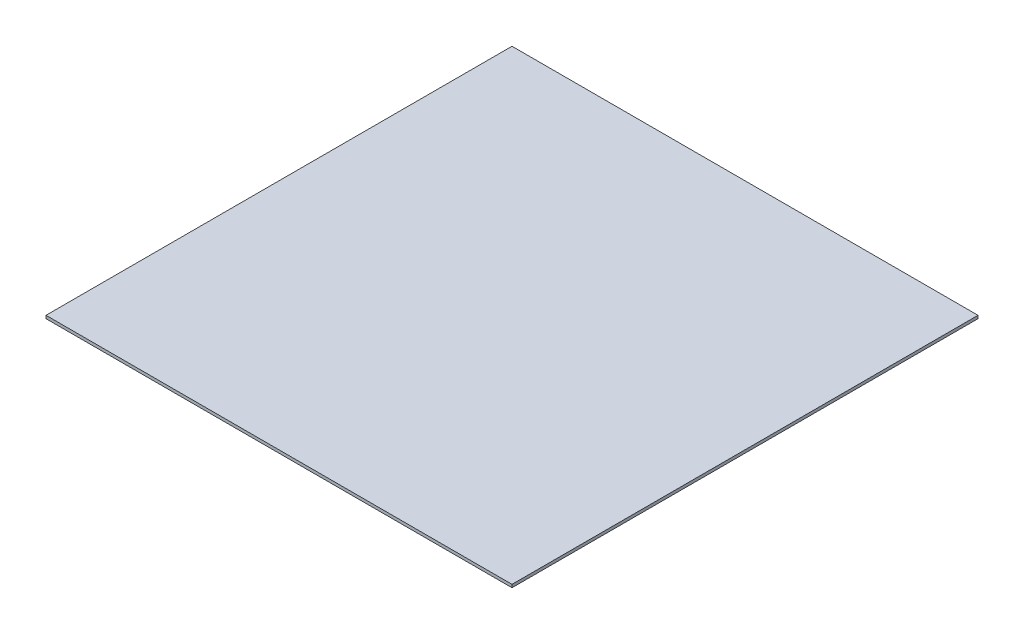
SolidWorks part; units mm, degrees
ref_plane "Front Plane" through (0, 0, 0) normal (0, 0, 1) x (1, 0, 0)
ref_plane "Top Plane" through (0, 0, 0) normal (0, 1, 0) x (1, 0, 0)
ref_plane "Right Plane" through (0, 0, 0) normal (1, 0, 0) x (0, 0, -1)
sketch "Sketch1" plane through (0, 0, 0) normal (0, 1, 0) x (1, 0, 0)
  line L1 (-46.354, 28.8652) -> (-6.354, 28.8652)
  line L2 (-46.354, 28.8652) -> (-46.354, -11.1348)
  line L3 (-46.354, -11.1348) -> (-6.354, -11.1348)
  line L4 (-6.354, 28.8652) -> (-6.354, -11.1348)
  dimension "D1" = 40
  dimension "D2" = 40
extrude "Boss-Extrude1" add sketch "Sketch1" along normal blind 0.254
